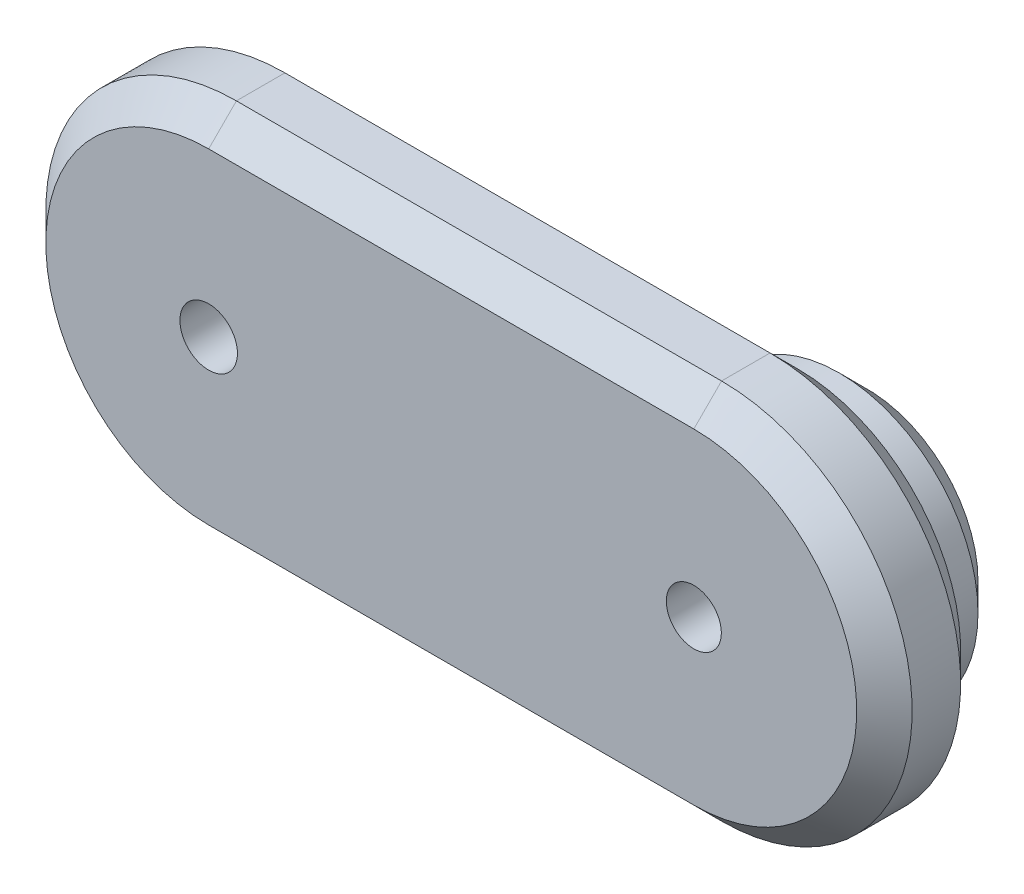
SolidWorks part; units mm, degrees
ref_plane "Front Plane" through (0, 0, 0) normal (0, 0, 1) x (1, 0, 0)
ref_plane "Top Plane" through (0, 0, 0) normal (0, 1, 0) x (1, 0, 0)
ref_plane "Right Plane" through (0, 0, 0) normal (1, 0, 0) x (0, 0, -1)
sketch "Sketch2" plane through (0, 0, 0) normal (0, 0, 1) x (1, 0, 0)
  line L0 (70, 27.5) -> (0, 27.5)
  line L3 (70, 0) -> (0, 0) construction
  line L6 (70, -27.5) -> (0, -27.5)
  circle A0 centre (0, 0) radius 18 construction
  circle A1 centre (0, 0) radius 4.15
  circle A5 centre (-18, 0) radius 2.25 construction
  arc A10 (0, 27.5) -> (0, -27.5) centre (0, 0) ccw
  circle A11 centre (70, 0) radius 38.1 construction
  circle A12 centre (-16.2174, 7.8099) radius 2.25 construction
  circle A13 centre (-11.2228, 14.073) radius 2.25 construction
  circle A14 centre (-4.0054, 17.5487) radius 2.25 construction
  circle A15 centre (4.0054, 17.5487) radius 2.25 construction
  circle A16 centre (11.2228, 14.073) radius 2.25 construction
  circle A17 centre (16.2174, 7.8099) radius 2.25 construction
  circle A18 centre (18, 0) radius 2.25 construction
  circle A19 centre (16.2174, -7.8099) radius 2.25 construction
  circle A20 centre (11.2228, -14.073) radius 2.25 construction
  circle A21 centre (4.0054, -17.5487) radius 2.25 construction
  circle A22 centre (-4.0054, -17.5487) radius 2.25 construction
  circle A23 centre (-11.2228, -14.073) radius 2.25 construction
  circle A24 centre (-16.2174, -7.8099) radius 2.25 construction
  circle A25 centre (70, 0) radius 3.9687
  arc A26 (70, -27.5) -> (70, 27.5) centre (70, 0) ccw
  dimension "D1" = 36
  dimension "D2" = 8.3
  dimension "D3" = 4.5
  dimension "D4" = 14
  dimension "D5" = 76.2
  dimension "D6" = 70
  dimension "D9" = 55
  dimension "D10" = 7.9375
extrude "Boss-Extrude1" add sketch "Sketch2" along normal blind 15
sketch "Sketch3" plane through (0, 0, 0) normal (0, 0, -1) x (-1, 0, 0)
  circle A0 centre (0, 0) radius 18 construction
  circle A1 centre (-18, 0) radius 2.25
  circle A2 centre (-16.2174, 7.8099) radius 2.25
  circle A3 centre (-11.2228, 14.073) radius 2.25
  circle A4 centre (-4.0054, 17.5487) radius 2.25
  circle A5 centre (4.0054, 17.5487) radius 2.25
  circle A6 centre (11.2228, 14.073) radius 2.25
  circle A7 centre (16.2174, 7.8099) radius 2.25
  circle A8 centre (18, 0) radius 2.25
  circle A9 centre (16.2174, -7.8099) radius 2.25
  circle A10 centre (11.2228, -14.073) radius 2.25
  circle A11 centre (4.0054, -17.5487) radius 2.25
  circle A12 centre (-4.0054, -17.5487) radius 2.25
  circle A13 centre (-11.2228, -14.073) radius 2.25
  circle A14 centre (-16.2174, -7.8099) radius 2.25
  point P34 (0, 0)
  dimension "D1" = 4.5
  dimension "D3" = 36
  dimension "D2" = 14
extrude "Boss-Extrude2" add sketch "Sketch3" along normal blind 2.25
chamfer "Chamfer1" distance 1.5 angle 45 14 edges at (13.9674, -7.8099, -2.25) (8.9728, -14.073, -2.25) (1.7554, -17.5487, -2.25) (-6.2554, -17.5487, -2.25) (-18.4674, -7.8099, -2.25) (-20.25, 0, -2.25) (-18.4674, 7.8099, -2.25) (-13.4728, 14.073, -2.25) (-6.2554, 17.5487, -2.25) (1.7554, 17.5487, -2.25) (8.9728, 14.073, -2.25) (13.9674, 7.8099, -2.25) (15.75, 0, -2.25) (-13.4728, -14.073, -2.25)
sketch "Sketch4" plane through (0, 0, 15) normal (0, 0, 1) x (1, 0, 0)
  circle A0 centre (0, 0) radius 4.15
  circle A1 centre (0, 0) radius 22.5
  dimension "D1" = 45
sketch "Sketch5" plane through (0, 0, 0) normal (0, 0, -1) x (-1, 0, 0)
  circle A0 centre (-70, 0) radius 3.9687
  circle A1 centre (-70, 0) radius 20
  circle A2 centre (-70, 0) radius 3.9687 construction
  dimension "D1" = 40
extrude "Boss-Extrude4" add sketch "Sketch5" along normal blind 10
chamfer "Chamfer2" distance 4 angle 45 1 edges at (50, 0, -10)
chamfer "Chamfer3" distance 4 angle 45 8 edges at (-27.5, 0, 15) (35, -27.5, 15) (35, 27.5, 15) (97.5, 0, 15) (-27.5, 0, 0) (35, -27.5, 0) (35, 27.5, 0) (97.5, 0, 0)
